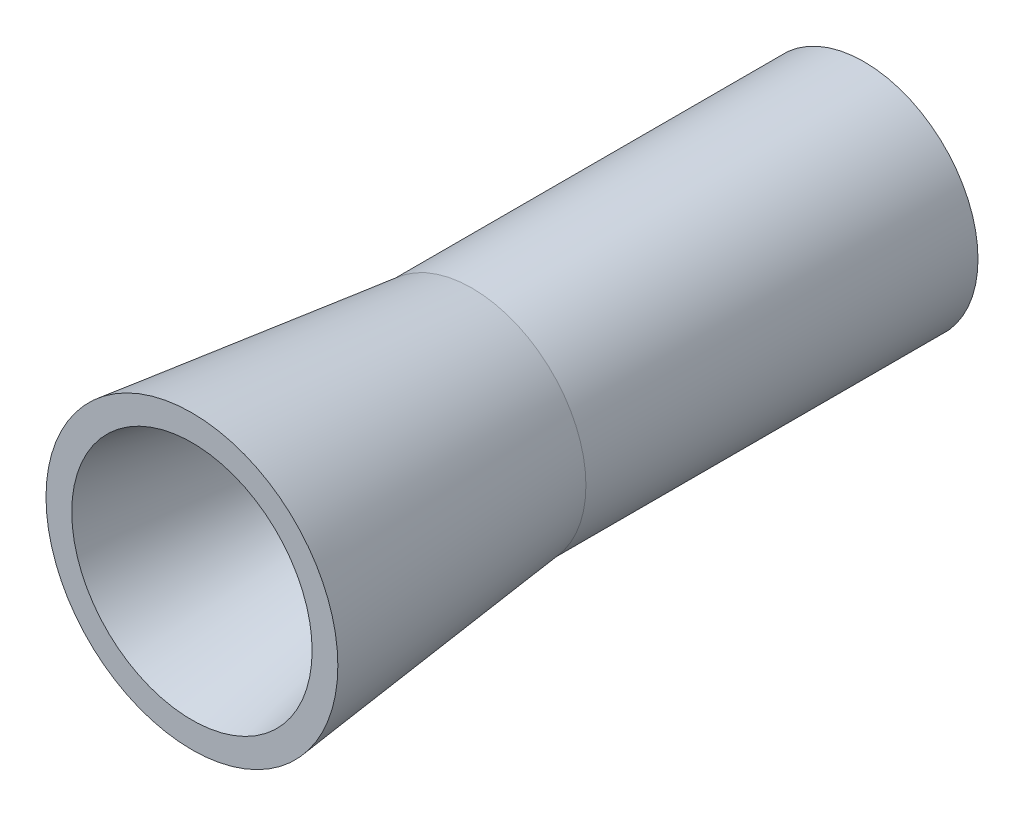
SolidWorks part; units mm, degrees
ref_plane "Front Plane" through (0, 0, 0) normal (0, 0, 1) x (1, 0, 0)
ref_plane "Top Plane" through (0, 0, 0) normal (0, 1, 0) x (1, 0, 0)
ref_plane "Right Plane" through (0, 0, 0) normal (1, 0, 0) x (0, 0, -1)
sketch "Sketch1" plane through (0, 0, 0) normal (1, 0, 0) x (0, 0, -1)
  line L0 (358.4801, 883.5084) -> (1791.1468, 883.5084) construction
  line L1 (1958.8047, 674.4008) -> (2053.3753, 658.9256)
  line L2 (2142.7875, 318.527) -> (2248.5003, 318.527)
  line L3 (2754.6337, 318.527) -> (-2754.6337, 318.527) construction
  line L4 (2326.7703, 318.527) -> (2428.4183, 318.527)
  line L5 (2509.0337, 318.527) -> (2602.4305, 318.527)
  line L6 (2689.7359, 318.527) -> (2777.7379, 318.527)
  line L7 (3260.7251, 318.527) -> (3337.6959, 318.527)
  line L8 (3393.7223, 318.527) -> (3481.1654, 318.527)
  line L9 (3528.2904, 318.527) -> (3609.4502, 318.527)
  line L10 (2443.8262, 375.8815) -> (2443.8262, 343.1066)
  line L11 (2443.8262, 343.1066) -> (2542.8481, 324.9759)
  line L12 (2542.8481, 324.9759) -> (2733.9186, 324.9759)
  line L13 (2733.9186, 324.9759) -> (2888.7274, 375.8815)
  line L14 (2888.7274, 375.8815) -> (2888.7274, 406.5643)
  line L15 (2888.7274, 406.5643) -> (2719.9718, 375.8815)
  line L16 (2719.9718, 375.8815) -> (2443.8262, 375.8815)
  point P2 (1958.8047, 674.4008)
  point P3 (2053.3753, 658.9256)
  point P4 (2142.7875, 643.4505)
  point P5 (2235.6387, 631.4142)
  point P6 (2326.7703, 612.5001)
  point P7 (2417.902, 598.7444)
  point P8 (2509.0337, 584.9886)
  point P9 (2602.4305, 573.3641)
  point P10 (2689.7359, 554.4873)
  point P11 (2785.2998, 545.0489)
  point P12 (1971.2366, 318.527)
  point P31 (3252.9128, 531.4222)
  point P32 (3393.7223, 564.5982)
  point P33 (3528.2904, 591.7422)
ref_plane "Plane1" through (0, 318.527, 0) normal (0, 1, 0) x (1, 0, 0)
sketch "Sketch55" plane through (0, 0, 0) normal (0, 1, 0) x (1, 0, 0)
  line L0 (0, 3798.472) -> (0, 3692.0528)
sketch "Sketch56" plane through (0, 0, 0) normal (1, 0, 0) x (0, 0, -1)
  line L0 (834.8716, 471.1565) -> (834.8716, -201.4799) construction
  line L1 (1614.3054, 257.5617) -> (660.6232, 257.5617) construction
  line L2 (954.2488, 397.5699) -> (954.2488, 372.8712)
  line L3 (954.2488, 372.8712) -> (1200.3543, 320.8274)
  line L4 (1200.3543, 320.8274) -> (1453.2467, 320.8274)
  line L5 (1453.2467, 320.8274) -> (1599.1305, 336.7133)
  line L6 (1599.1305, 336.7133) -> (1599.1305, 366.8546)
  line L7 (1599.1305, 366.8546) -> (1222.9672, 366.8546)
  line L8 (1222.9672, 366.8546) -> (954.2488, 397.5699)
revolve "Revolve1" add sketch "Sketch56" angle 360 about L1
